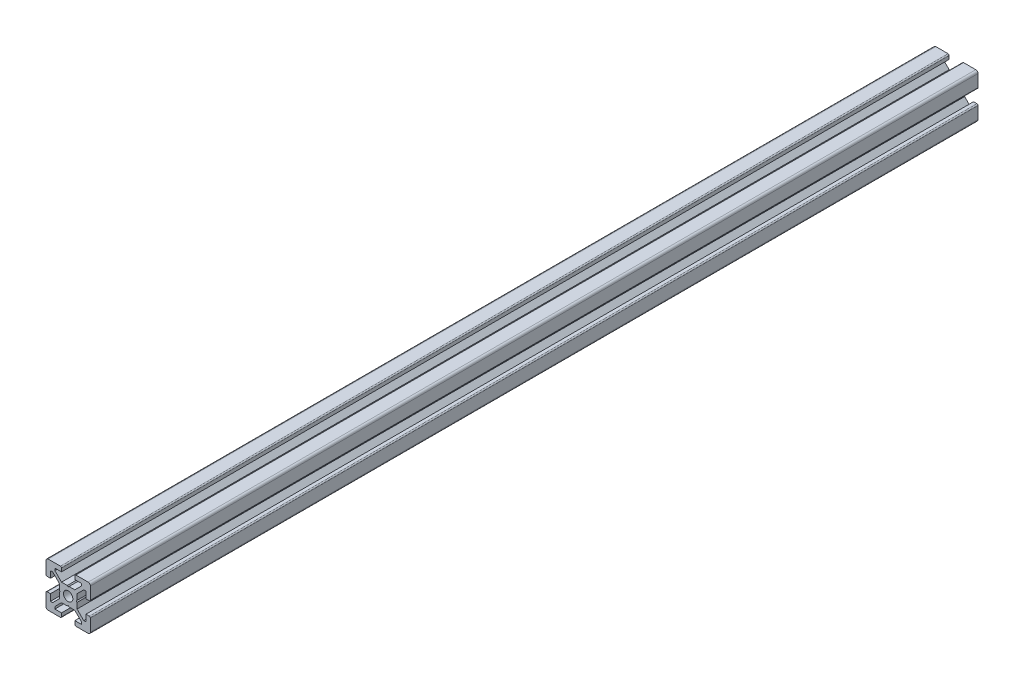
SolidWorks part; units mm, degrees
material "Lega 6061"
ref_plane "Piano frontale" through (0, 0, 0) normal (0, 0, 1) x (1, 0, 0)
ref_plane "Piano superiore" through (0, 0, 0) normal (0, 1, 0) x (1, 0, 0)
ref_plane "Piano destro" through (0, 0, 0) normal (1, 0, 0) x (0, 0, -1)
sketch "Schizzo1" plane through (0, 0, 0) normal (0, 0, 1) x (1, 0, 0)
  line L0 (0, 0) -> (-10, 0) construction
  line L1 (0, 0) -> (0, 10) construction
  line L2 (-3.6, 0) -> (-4, 0.4)
  line L3 (-4, 0.4) -> (-4, 3)
  line L4 (-4, 3) -> (-7, 6)
  line L5 (-7, 6) -> (-8, 6)
  line L6 (-8, 6) -> (-8, 3)
  line L7 (-8, 3) -> (-9.5, 3)
  line L8 (-10, 3.5) -> (-10, 9)
  line L9 (0, 0) -> (-10, 10) construction
  line L10 (0, 3.6) -> (-0.4, 4)
  line L11 (-0.4, 4) -> (-3, 4)
  line L12 (-3, 4) -> (-6, 7)
  line L13 (-6, 7) -> (-6, 8)
  line L14 (-6, 8) -> (-3, 8)
  line L15 (-3, 8) -> (-3, 9.5)
  line L16 (-3.5, 10) -> (-9, 10)
  line L17 (0, 0) -> (-10, -10) construction
  line L18 (-3.5, -10) -> (-9, -10)
  line L19 (-3, -8) -> (-3, -9.5)
  line L20 (-6, -8) -> (-3, -8)
  line L21 (-6, -7) -> (-6, -8)
  line L22 (-3, -4) -> (-6, -7)
  line L23 (-0.4, -4) -> (-3, -4)
  line L24 (0, -3.6) -> (-0.4, -4)
  line L25 (-10, -3.5) -> (-10, -9)
  line L26 (-8, -3) -> (-9.5, -3)
  line L27 (-8, -6) -> (-8, -3)
  line L28 (-7, -6) -> (-8, -6)
  line L29 (-4, -3) -> (-7, -6)
  line L30 (-4, -0.4) -> (-4, -3)
  line L31 (-3.6, 0) -> (-4, -0.4)
  line L32 (0, 0) -> (10, -10) construction
  line L33 (0, 0) -> (10, 10) construction
  line L34 (3.6, 0) -> (4, -0.4)
  line L35 (4, -0.4) -> (4, -3)
  line L36 (4, -3) -> (7, -6)
  line L37 (7, -6) -> (8, -6)
  line L38 (8, -6) -> (8, -3)
  line L39 (8, -3) -> (9.5, -3)
  line L40 (10, -3.5) -> (10, -9)
  line L41 (0, -3.6) -> (0.4, -4)
  line L42 (0.4, -4) -> (3, -4)
  line L43 (3, -4) -> (6, -7)
  line L44 (6, -7) -> (6, -8)
  line L45 (6, -8) -> (3, -8)
  line L46 (3, -8) -> (3, -9.5)
  line L47 (3.5, -10) -> (9, -10)
  line L48 (3.5, 10) -> (9, 10)
  line L49 (3, 8) -> (3, 9.5)
  line L50 (6, 8) -> (3, 8)
  line L51 (6, 7) -> (6, 8)
  line L52 (3, 4) -> (6, 7)
  line L53 (0.4, 4) -> (3, 4)
  line L54 (0, 3.6) -> (0.4, 4)
  line L55 (10, 3.5) -> (10, 9)
  line L56 (8, 3) -> (9.5, 3)
  line L57 (8, 6) -> (8, 3)
  line L58 (7, 6) -> (8, 6)
  line L59 (4, 3) -> (7, 6)
  line L60 (4, 0.4) -> (4, 3)
  line L61 (3.6, 0) -> (4, 0.4)
  arc A0 (-10, 9) -> (-9, 10) centre (-9, 9) cw
  arc A1 (-3, 9.5) -> (-3.5, 10) centre (-3.5, 9.5) ccw
  arc A2 (-9.5, 3) -> (-10, 3.5) centre (-9.5, 3.5) cw
  arc A3 (-9.5, -3) -> (-10, -3.5) centre (-9.5, -3.5) ccw
  arc A4 (-3, -9.5) -> (-3.5, -10) centre (-3.5, -9.5) cw
  arc A5 (-10, -9) -> (-9, -10) centre (-9, -9) ccw
  arc A6 (10, -9) -> (9, -10) centre (9, -9) cw
  arc A7 (3, -9.5) -> (3.5, -10) centre (3.5, -9.5) ccw
  arc A8 (9.5, -3) -> (10, -3.5) centre (9.5, -3.5) cw
  arc A9 (9.5, 3) -> (10, 3.5) centre (9.5, 3.5) ccw
  arc A10 (3, 9.5) -> (3.5, 10) centre (3.5, 9.5) cw
  arc A11 (10, 9) -> (9, 10) centre (9, 9) ccw
  circle A12 centre (0, 0) radius 2.1
  point P24 (-3, 10)
  point P27 (-10, 3)
  point P49 (-10, -3)
  point P50 (-3, -10)
  point P92 (3, -10)
  point P93 (10, -3)
  point P94 (10, 3)
  point P95 (3, 10)
  dimension "D2" = 1
  dimension "D12" = 0.5
  dimension "D13" = 4.2
  dimension "D3" = 8
  dimension "D4" = 0.4
  dimension "D5" = 45
  dimension "D6" = 6
  dimension "D7" = 12
  dimension "D8" = 20
  dimension "D9" = 2
  dimension "D10" = 4
  dimension "D11" = 45
extrude "Estrusione-Estrusione1" add sketch "Schizzo1" along normal blind 400
